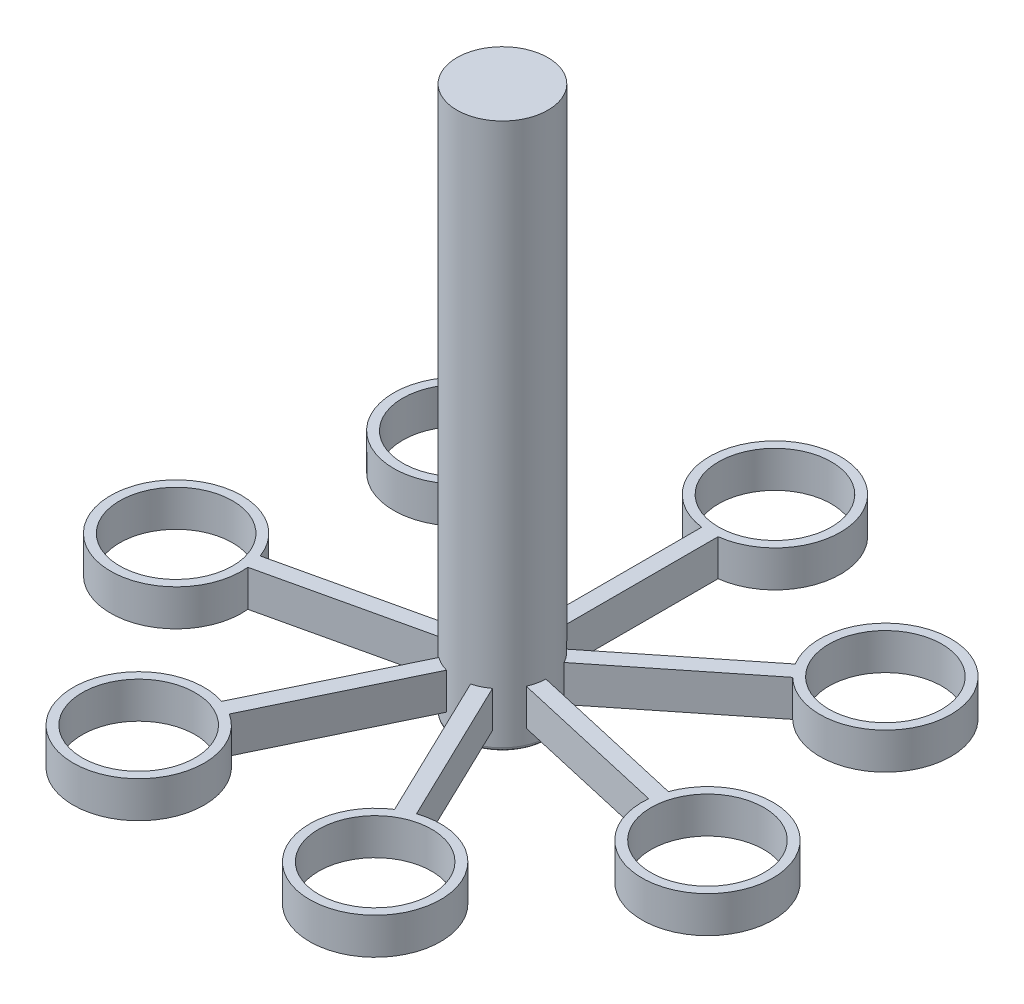
SolidWorks part; units mm, degrees
ref_plane "Front Plane" through (0, 0, 0) normal (0, 0, 1) x (1, 0, 0)
ref_plane "Top Plane" through (0, 0, 0) normal (0, 1, 0) x (1, 0, 0)
ref_plane "Right Plane" through (0, 0, 0) normal (1, 0, 0) x (0, 0, -1)
sketch "Sketch1" plane through (0, 0, 0) normal (0, 1, 0) x (1, 0, 0)
  circle A0 centre (0, 0) radius 12.5
  dimension "D1" = 25
extrude "Boss-Extrude1" add sketch "Sketch1" along normal blind 150
sketch "Sketch3" plane through (0, 0, 0) normal (0, 1, 0) x (1, 0, 0)
  line L3 (-2.2538, 56.9474) -> (-2.2538, 12.2951)
  line L4 (2.2538, 56.9474) -> (2.2538, 12.2951)
  line L5 (-2.2538, 12.2951) -> (2.2538, 12.2951)
  line L6 (0, 12.2951) -> (0, 0) construction
  arc A1 (2.2538, 56.9474) -> (-2.2538, 56.9474) centre (0, 74.8057) ccw
  circle A3 centre (0, 0) radius 12.5 construction
  circle A4 centre (0, 74.8057) radius 15.5
  point P11 (0, 12.2951)
  dimension "D1" = 18
  dimension "D2" = 31
extrude "Boss-Extrude2" add sketch "Sketch3" along normal blind 10 from offset 5
pattern_circular "CirPattern1" count 7 over 360 about axis through (0, 0, 0) along (0, 1, 0) of "Boss-Extrude2"
fillet "Fillet1" radius 1 1 edges at (0, 0, 12.5)
